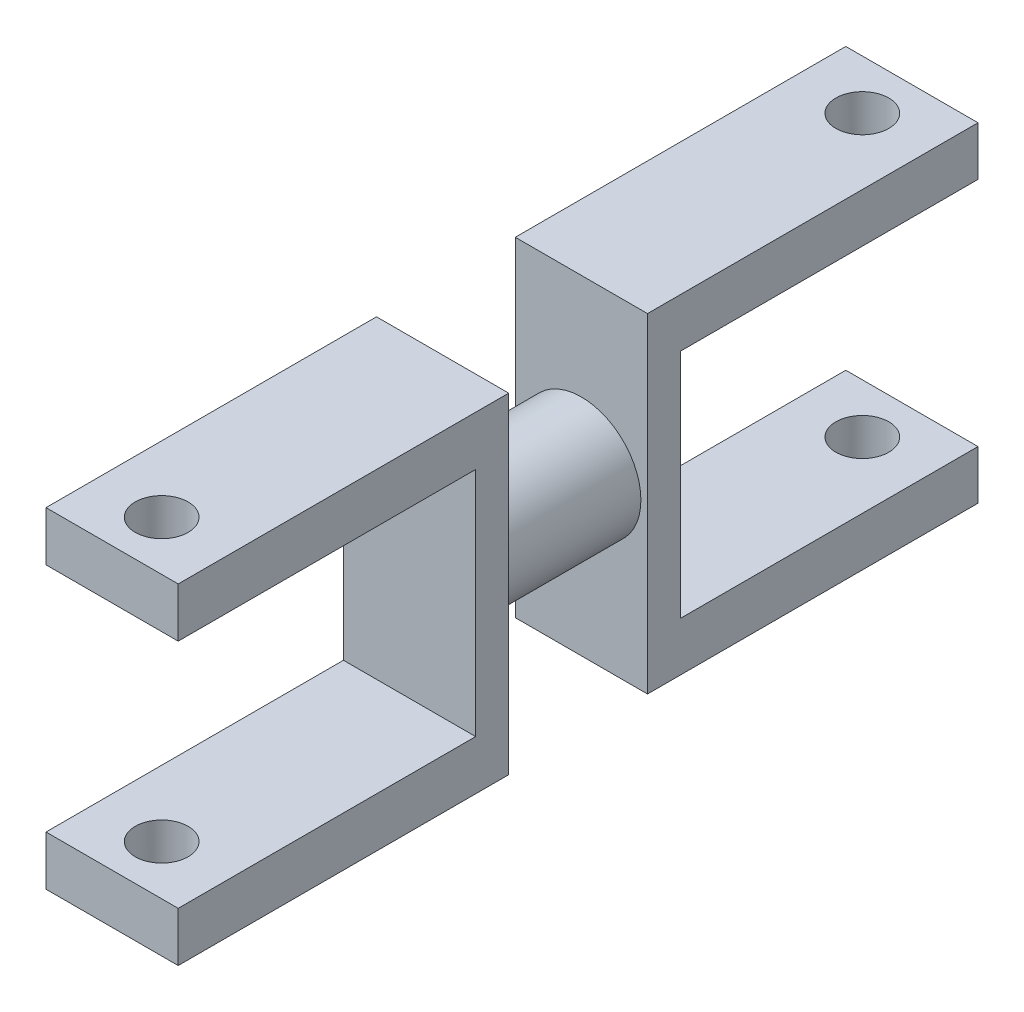
SolidWorks part; units mm, degrees
ref_plane "前视基准面" through (0, 0, 0) normal (0, 0, 1) x (1, 0, 0)
ref_plane "上视基准面" through (0, 0, 0) normal (0, 1, 0) x (1, 0, 0)
ref_plane "右视基准面" through (0, 0, 0) normal (1, 0, 0) x (0, 0, -1)
sketch "草图1" plane through (0, 0, 0) normal (0, 0, 1) x (1, 0, 0)
  circle A0 centre (0, 0) radius 2.8
  circle A1 centre (0, 0) radius 3.6
extrude "凸台-拉伸1" add sketch "草图1" along normal blind 8.4 contours A1
sketch "草图2" plane through (0, 0, 0) normal (0, 0, -1) x (-1, 0, 0)
  line L1 (-4, 9.9696) -> (4, 9.9696)
  line L2 (-4, 9.9696) -> (-4, -9.9696)
  line L3 (-4, -9.9696) -> (4, -9.9696)
  line L4 (4, 9.9696) -> (4, -9.9696)
  line L5 (-4, 9.9696) -> (4, -9.9696) construction
  line L6 (-4, -9.9696) -> (4, 9.9696) construction
  point P0 (0, 0)
extrude "凸台-拉伸2" add sketch "草图2" along normal blind 20 contours L3 L4 L1 L2
sketch "草图3" plane through (0, 0, 8.4) normal (0, 0, 1) x (1, 0, 0)
  line L1 (-4, 10) -> (4, 10)
  line L2 (-4, 10) -> (-4, -10)
  line L3 (-4, -10) -> (4, -10)
  line L4 (4, 10) -> (4, -10)
  line L5 (-4, 10) -> (4, -10) construction
  line L6 (-4, -10) -> (4, 10) construction
  point P0 (0, 0)
extrude "凸台-拉伸3" add sketch "草图3" along normal blind 20
sketch "草图4" plane through (0, 0, -20) normal (0, 0, -1) x (-1, 0, 0)
  line L0 (-4, 9.9696) -> (-4, 7)
  line L1 (-4, 9.9696) -> (-4, -9.9696) construction
  line L2 (4, -9.9696) -> (4, -7)
  line L3 (4, 9.9696) -> (4, -9.9696) construction
  line L5 (-4, 7) -> (4, 7)
  line L6 (-4, 7) -> (-4, -7)
  line L7 (-4, -7) -> (4, -7)
  line L8 (4, 7) -> (4, -7)
  line M2 (-4, 9.9696) -> (-4, -9.9696)
  line M4 (4, -9.9696) -> (4, 9.9696)
extrude "切除-拉伸2" cut sketch "草图4" against normal blind 18 contours L7 L5 M2 M4
sketch "草图5" plane through (0, 0, 28.4) normal (0, 0, 1) x (1, 0, 0)
  line L0 (-4, 10) -> (-4, 7)
  line L1 (-4, 10) -> (-4, -10) construction
  line L2 (4, -10) -> (4, -7)
  line L3 (4, -10) -> (4, 10) construction
  line L5 (-4, 7) -> (4, 7)
  line L6 (-4, 7) -> (-4, -7)
  line L7 (-4, -7) -> (4, -7)
  line L8 (4, 7) -> (4, -7)
  line M1 (4, -10) -> (4, 10)
  line M3 (-4, 10) -> (-4, -10)
extrude "切除-拉伸3" cut sketch "草图5" against normal blind 18 contours L7 L5 M3 M1
sketch "草图6" plane through (0, 9.9696, 0) normal (0, 1, 0) x (1, 0, 0)
  line L0 (0, 20) -> (0, 17)
  line L1 (4, 20) -> (-4, 20) construction
  line L2 (0, -28.4) -> (0, -25.4)
  line L3 (4, -28.4) -> (-4, -28.4) construction
  circle A0 centre (0, 17) radius 1.6
  circle A1 centre (0, -25.4) radius 1.6
extrude "切除-拉伸4" cut sketch "草图6" against normal blind 29 and the other way blind 10
